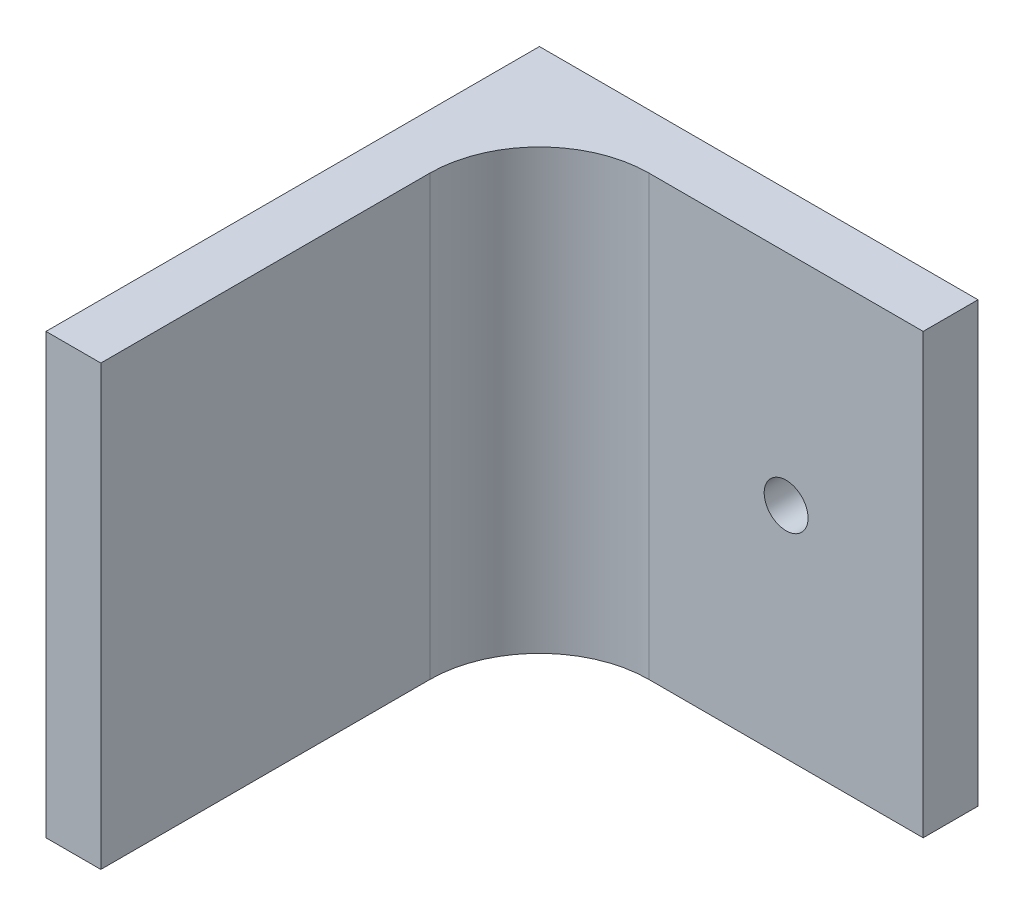
SolidWorks part; units mm, degrees
ref_plane "Front Plane" through (0, 0, 0) normal (0, 0, 1) x (1, 0, 0)
ref_plane "Top Plane" through (0, 0, 0) normal (0, 1, 0) x (1, 0, 0)
ref_plane "Right Plane" through (0, 0, 0) normal (1, 0, 0) x (0, 0, -1)
sketch "Sketch2" plane through (0, 0, 0) normal (0, 0, 1) x (1, 0, 0)
  line L0 (67.999, 8.4848) -> (105.2711, 8.4848) construction
  line L1 (67.999, 40.9848) -> (67.999, -24.0152) construction
  line L3 (67.999, 18.4848) -> (87.999, 18.4848)
  line L4 (67.999, 18.4848) -> (67.999, -1.5152)
  line L5 (67.999, -1.5152) -> (87.999, -1.5152)
  line L6 (87.999, 18.4848) -> (87.999, -1.5152)
  dimension "D1" = 10
  dimension "D2" = 10
  dimension "D3" = 20
extrude "Boss-Extrude1" add sketch "Sketch2" along normal blind 2.5
sketch "Sketch3" plane through (0, 0, 0) normal (0, 0, 1) x (1, 0, 0)
  line L0 (87.999, 18.4848) -> (67.999, 18.4848) construction
  line L1 (67.999, -1.5152) -> (70.499, -1.5152)
  line L2 (67.999, -1.5152) -> (67.999, 18.4848)
  line L3 (67.999, 18.4848) -> (70.499, 18.4848)
  line L4 (70.499, -1.5152) -> (70.499, 18.4848)
  dimension "D1" = 2.5
extrude "Boss-Extrude2" add sketch "Sketch3" along normal blind 22.5
fillet "Fillet1" radius 5 1 edges at (70.499, 8.4848, 2.5)
sketch "Sketch4" plane through (0, 0, 2.5) normal (0, 0, 1) x (1, 0, 0)
  line L0 (75.499, 18.4848) -> (87.999, -1.5152) construction
  line L1 (87.999, 18.4848) -> (75.499, -1.5152) construction
  circle A0 centre (81.749, 8.4848) radius 1
  dimension "D1" = 2
extrude "Cut-Extrude1" cut sketch "Sketch4" against normal blind 22.5
